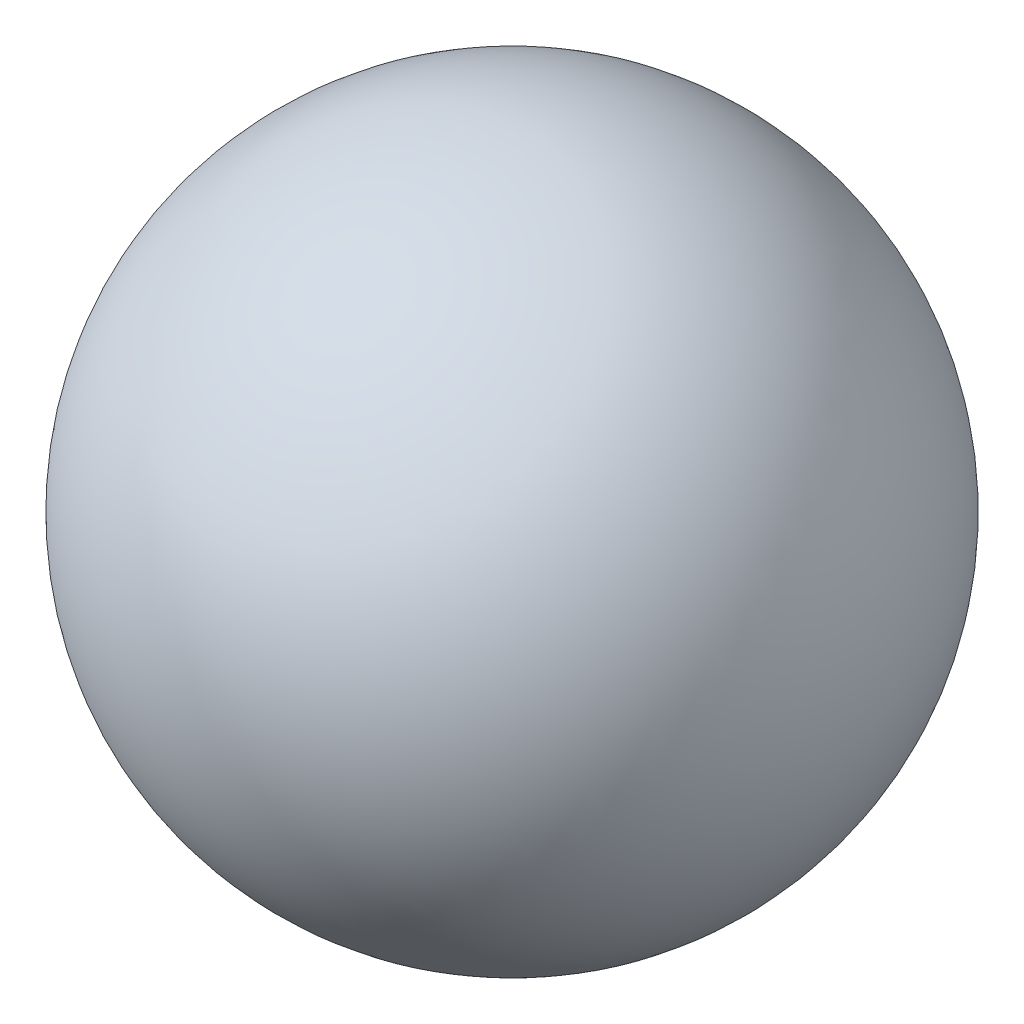
SolidWorks part; units mm, degrees
ref_plane "Front Plane" through (0, 0, 0) normal (0, 0, 1) x (1, 0, 0)
ref_plane "Top Plane" through (0, 0, 0) normal (0, 1, 0) x (1, 0, 0)
ref_plane "Right Plane" through (0, 0, 0) normal (1, 0, 0) x (0, 0, -1)
sketch "Sketch1" plane through (0, 0, 0) normal (0, 0, 1) x (1, 0, 0)
  line L0 (0, 410.6166) -> (0, -410.6166)
  arc A0 (0, -410.6166) -> (0, 410.6166) centre (0, 0) ccw
  dimension "D1" = 821.2331
revolve "Revolve1" add sketch "Sketch1" angle 360 about L0
